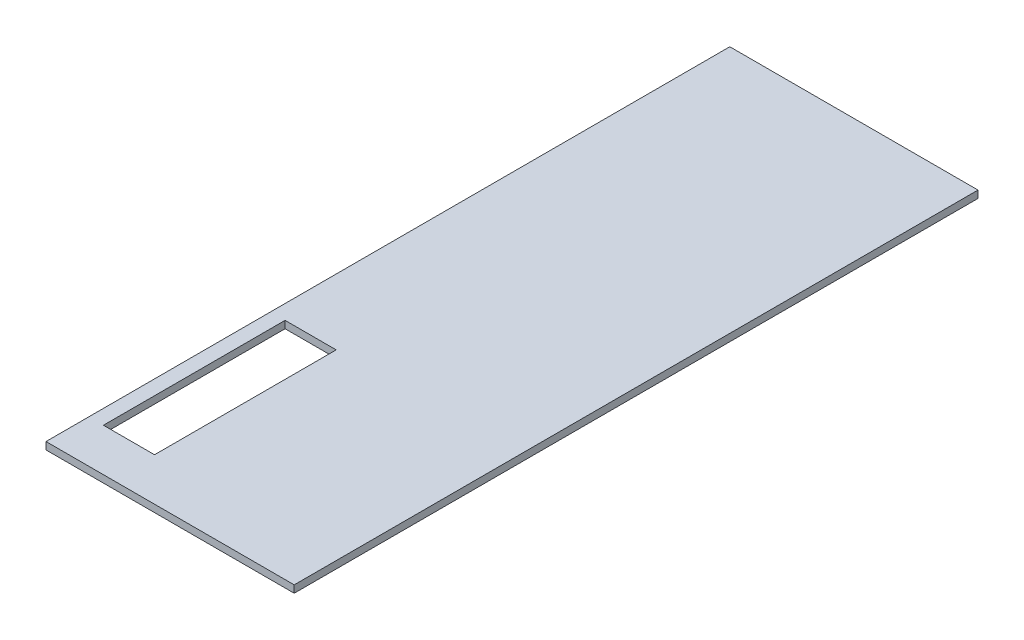
SolidWorks part; units mm, degrees
material "混凝土"
ref_plane "前视基准面" through (0, 0, 0) normal (0, 0, 1) x (1, 0, 0)
ref_plane "上视基准面" through (0, 0, 0) normal (0, 1, 0) x (1, 0, 0)
ref_plane "右视基准面" through (0, 0, 0) normal (1, 0, 0) x (0, 0, -1)
sketch "草图1" plane through (0, 0, 0) normal (0, 1, 0) x (1, 0, 0)
  line L0 (-2040, 5620) -> (2040, -5620) construction
  line L1 (2040, -5620) -> (-2040, -5620)
  line L2 (2040, -5620) -> (2040, 5620)
  line L3 (2040, 5620) -> (-2040, 5620)
  line L4 (-2040, -5620) -> (-2040, 5620)
  line L5 (-2040, -5620) -> (2040, 5620) construction
  dimension "D1" = 4080
  dimension "D2" = 11240
extrude "凸台-拉伸1" add sketch "草图1" against normal blind 120
sketch "草图2" plane through (0, -120, 0) normal (0, -1, 0) x (1, 0, 0)
  line L0 (-1800, 1930) -> (-1800, 4915.8677)
  line L2 (-1800, 4915.8677) -> (-960, 4915.8677)
  line L3 (-960, 4915.8677) -> (-960, 1930)
  line L4 (-960, 1930) -> (-1800, 1930)
  line L5 (-1800, 930) -> (1800, 930) construction
  line L8 (-880, 4915.8677) -> (-1800, 4915.8677) construction
  line L9 (-1800, 930) -> (-1800, 4780) construction
  line L10 (-960, 2900) -> (-960, 4780) construction
  dimension "D1" = 1000
extrude "梯口" cut sketch "草图2" against normal through all
